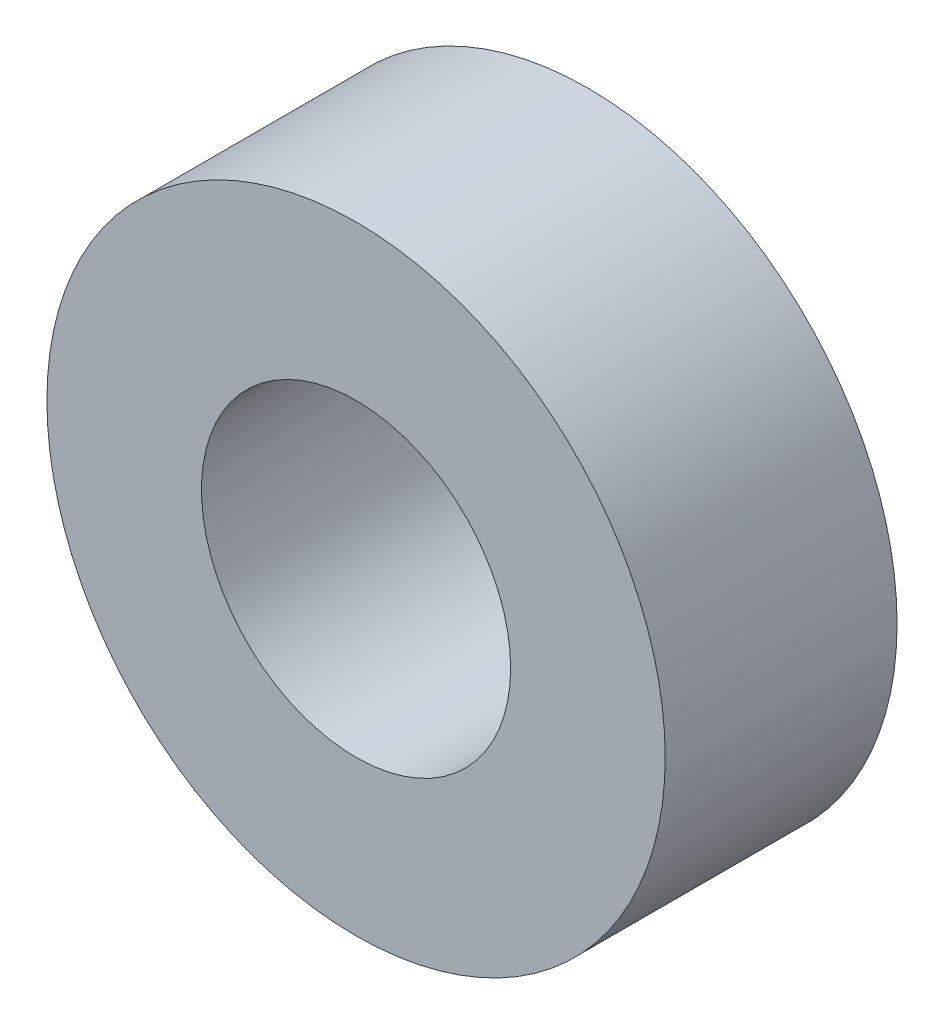
SolidWorks part; units mm, degrees
material "Alliage 7079"
ref_plane "Face" through (0, 0, 0) normal (0, 0, 1) x (1, 0, 0)
ref_plane "Dessus" through (0, 0, 0) normal (0, 1, 0) x (1, 0, 0)
ref_plane "Droite" through (0, 0, 0) normal (1, 0, 0) x (0, 0, -1)
sketch "Esquisse1" plane through (0, 0, 0) normal (0, 0, 1) x (1, 0, 0)
  circle A0 centre (0, 0) radius 2
  circle A1 centre (0, 0) radius 4
  dimension "D1" = 4
  dimension "D2" = 8
extrude "Extrusion1" add sketch "Esquisse1" along normal blind 3
